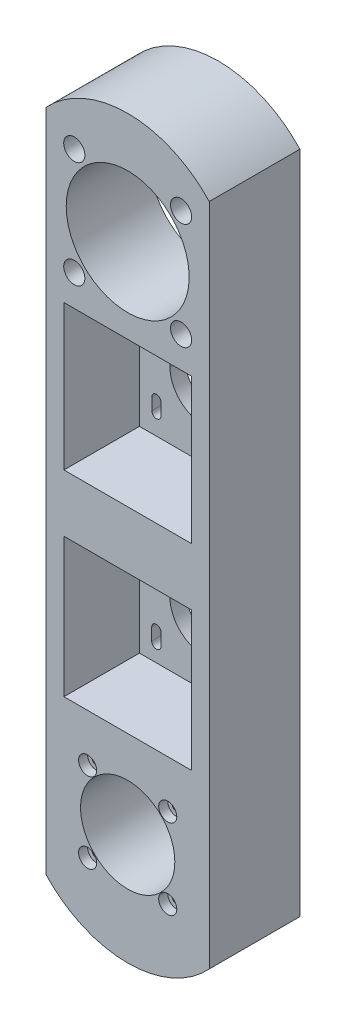
SolidWorks part; units mm, degrees
ref_plane "前视基准面" through (0, 0, 0) normal (0, 0, 1) x (1, 0, 0)
ref_plane "上视基准面" through (0, 0, 0) normal (0, 1, 0) x (1, 0, 0)
ref_plane "右视基准面" through (0, 0, 0) normal (1, 0, 0) x (0, 0, -1)
sketch "草图1" plane through (0, 0, 0) normal (0, 0, 1) x (1, 0, 0)
  line L1 (-27, 110) -> (27, 110)
  line L2 (-27, 110) -> (-27, -110)
  line L3 (-27, -110) -> (27, -110)
  line L4 (27, 110) -> (27, -110)
  line L5 (0, -110) -> (0, 110) construction
  line L6 (-27, 0) -> (27, 0) construction
  point P0 (0, 0)
  dimension "D1" = 220
  dimension "D2" = 54
extrude "凸台-拉伸1" add sketch "草图1" along normal blind 30
sketch "草图2" plane through (0, 0, 30) normal (0, 0, 1) x (1, 0, 0)
  line L0 (0, 99) -> (0, -113.7312) construction
  line L1 (-21.1, 57) -> (21.1, 57)
  line L2 (-21.1, 57) -> (-21.1, 9)
  line L3 (-21.1, 9) -> (21.1, 9)
  line L4 (21.1, 57) -> (21.1, 9)
  line L5 (0, 9) -> (0, 57) construction
  line L6 (-21.1, 33) -> (21.1, 33) construction
  line L7 (27, 110) -> (-27, 110) construction
  line L12 (0, 53) -> (0, 95) construction
  line L13 (-21, 85) -> (21, 85) construction
  point P0 (0, 33)
  point P6 (0, 85)
  dimension "D1" = 48
  dimension "D2" = 42.2
  dimension "D3" = 25
  dimension "D4" = 52
extrude "切除-拉伸1" cut sketch "草图2" against normal offset from surface (25 mm away) 5 up to face at (0, 0, 0)
sketch "草图3" plane through (0, 0, 30) normal (0, 0, -1) x (-1, 0, 0)
  line L0 (0, 105.3067) -> (0, -113.1294) construction
  line L1 (-21.1, -10) -> (21.1, -10)
  line L2 (-21.1, -10) -> (-21.1, -56)
  line L3 (-21.1, -56) -> (21.1, -56)
  line L4 (21.1, -10) -> (21.1, -56)
  line L5 (0, -56) -> (0, -10) construction
  line L6 (-21.1, -33) -> (21.1, -33) construction
  line L7 (27, -110) -> (-27, -110) construction
  line L12 (0, -95) -> (0, -53) construction
  line L13 (-21, -85) -> (21, -85) construction
  point P0 (0, -33)
  point P6 (0, -85)
  dimension "D1" = 46
  dimension "D2" = 42.2
  dimension "D3" = 25
  dimension "D4" = 52
extrude "切除-拉伸2" cut sketch "草图3" along normal offset from surface (25 mm away) 5 up to face at (0, 0, 0)
sketch "草图4" plane through (0, 0, 5) normal (0, 0, 1) x (1, 0, 0)
  line L0 (0, 33) -> (40.432, 33) construction
  line L1 (0, 0) -> (0, -107.9783) construction
  line L2 (-21.1, 57) -> (21.1, 57) construction
  line L3 (-21.1, 9) -> (21.1, 57) construction
  line L4 (21.1, 57) -> (21.1, 9) construction
  line L5 (-21.1, 57) -> (21.1, 9) construction
  line L6 (0, 35) -> (0, 31) construction
  line L7 (11, 35) -> (11, 31)
  line L8 (-11, 35) -> (-11, 31)
  line L9 (-15.5, 50.5) -> (-15.5, 46.5) construction
  line L10 (-14, 50.5) -> (-14, 46.5)
  line L11 (-17, 50.5) -> (-17, 46.5)
  line L12 (0, 33) -> (0, 63.0659) construction
  line L14 (15.5, 50.5) -> (15.5, 46.5) construction
  line L15 (14, 50.5) -> (14, 46.5)
  line L16 (17, 50.5) -> (17, 46.5)
  line L17 (15.5, 15.5) -> (15.5, 19.5) construction
  line L18 (14, 15.5) -> (14, 19.5)
  line L19 (17, 15.5) -> (17, 19.5)
  line L20 (-15.5, 15.5) -> (-15.5, 19.5) construction
  line L21 (-14, 15.5) -> (-14, 19.5)
  line L22 (-17, 15.5) -> (-17, 19.5)
  arc A17 (11, 35) -> (-11, 35) centre (0, 35) ccw
  arc A18 (-11, 31) -> (11, 31) centre (0, 31) ccw
  arc A19 (-14, 50.5) -> (-17, 50.5) centre (-15.5, 50.5) ccw
  arc A20 (-17, 46.5) -> (-14, 46.5) centre (-15.5, 46.5) ccw
  arc A21 (14, 50.5) -> (17, 50.5) centre (15.5, 50.5) cw
  arc A22 (17, 46.5) -> (14, 46.5) centre (15.5, 46.5) cw
  arc A23 (14, 15.5) -> (17, 15.5) centre (15.5, 15.5) ccw
  arc A24 (17, 19.5) -> (14, 19.5) centre (15.5, 19.5) ccw
  arc A25 (-14, 15.5) -> (-17, 15.5) centre (-15.5, 15.5) cw
  arc A26 (-17, 19.5) -> (-14, 19.5) centre (-15.5, 19.5) cw
  point P12 (0, 33)
  point P15 (0, 33)
  point P22 (-15.5, 48.5)
  point P32 (15.5, 48.5)
  point P39 (15.5, 17.5)
  point P46 (-15.5, 17.5)
  dimension "D1" = 4
  dimension "D4" = 4
  dimension "D3" = 1.5
  dimension "D6" = 11
  dimension "D2" = 15.5
  dimension "D5" = 15.5
extrude "切除-拉伸3" cut sketch "草图4" against normal through all
sketch "草图18" plane through (0, 0, 0) normal (0, 0, 1) x (1, 0, 0)
  line L1 (-16.1, -68.9) -> (16.1, -68.9)
  line L2 (-16.1, -68.9) -> (-16.1, -101.1)
  line L3 (-16.1, -101.1) -> (16.1, -101.1)
  line L4 (16.1, -68.9) -> (16.1, -101.1)
  line L5 (0, -101.1) -> (0, -68.9) construction
  line L6 (-16.1, -85) -> (16.1, -85) construction
  point P0 (0, -85)
  dimension "D1" = 32.2
  dimension "D2" = 32.2
sketch "草图26" plane through (0, 0, 5) normal (0, 0, 1) x (1, 0, 0)
  line L0 (-21.1, -56) -> (21.1, -10) construction
  line L1 (-21.1, -10) -> (21.1, -56) construction
  line L2 (0, -31) -> (0, -35) construction
  line L3 (21.1, -33) -> (-21.1, -33) construction
  line L4 (0, 99) -> (0, -113.7312) construction
  line L5 (11, -31) -> (11, -35)
  line L6 (-11, -31) -> (-11, -35)
  line L7 (-15.5, -15.5) -> (-15.5, -19.5) construction
  line L8 (-13.95, -15.5) -> (-13.95, -19.5)
  line L9 (-17.05, -15.5) -> (-17.05, -19.5)
  line L10 (0, -33) -> (45.7169, -33) construction
  line L11 (0, -33) -> (0, -41.2979) construction
  line L12 (-15.5, -50.5) -> (-15.5, -46.5) construction
  line L13 (-13.95, -50.5) -> (-13.95, -46.5)
  line L14 (-17.05, -50.5) -> (-17.05, -46.5)
  line L15 (15.5, -50.5) -> (15.5, -46.5) construction
  line L16 (13.95, -50.5) -> (13.95, -46.5)
  line L17 (17.05, -50.5) -> (17.05, -46.5)
  line L18 (15.5, -15.5) -> (15.5, -19.5) construction
  line L19 (13.95, -15.5) -> (13.95, -19.5)
  line L20 (17.05, -15.5) -> (17.05, -19.5)
  arc A0 (11, -31) -> (-11, -31) centre (0, -31) ccw
  arc A1 (-11, -35) -> (11, -35) centre (0, -35) ccw
  arc A2 (-13.95, -15.5) -> (-17.05, -15.5) centre (-15.5, -15.5) ccw
  arc A3 (-17.05, -19.5) -> (-13.95, -19.5) centre (-15.5, -19.5) ccw
  arc A4 (-13.95, -50.5) -> (-17.05, -50.5) centre (-15.5, -50.5) cw
  arc A5 (-17.05, -46.5) -> (-13.95, -46.5) centre (-15.5, -46.5) cw
  arc A6 (13.95, -50.5) -> (17.05, -50.5) centre (15.5, -50.5) ccw
  arc A7 (17.05, -46.5) -> (13.95, -46.5) centre (15.5, -46.5) ccw
  arc A8 (13.95, -15.5) -> (17.05, -15.5) centre (15.5, -15.5) cw
  arc A9 (17.05, -19.5) -> (13.95, -19.5) centre (15.5, -19.5) cw
  point P8 (0, -33)
  point P16 (0, -33)
  point P23 (-15.5, -17.5)
  point P34 (-15.5, -48.5)
  point P41 (15.5, -48.5)
  point P48 (15.5, -17.5)
  dimension "D2" = 11
  dimension "D4" = 1.55
  dimension "D1" = 4
  dimension "D3" = 4
  dimension "D5" = 15.5
  dimension "D6" = 15.5
extrude "切除-拉伸13" cut sketch "草图26" against normal through all
extrude "切除-拉伸9" cut sketch "草图18" along normal blind 6
sketch "草图9" plane through (0, 0, 6) normal (0, 0, 1) x (1, 0, 0)
  line L0 (16.1, -85) -> (-16.1, -85) construction
  line L3 (0, -68.9) -> (0, -101.1) construction
  line L6 (-16.1, -68.9) -> (16.1, -68.9) construction
  line L8 (16.1, -101.1) -> (-16.1, -101.1) construction
  line L9 (-16.1, -101.1) -> (-16.1, -68.9) construction
  line L10 (16.1, -68.9) -> (16.1, -101.1) construction
  circle A1 centre (0, -85) radius 15.6
  circle A2 centre (-13.2583, -71.7417) radius 1.6
  circle A3 centre (13.2583, -71.7417) radius 1.6
  circle A4 centre (13.2583, -98.2583) radius 1.6
  circle A5 centre (-13.2583, -98.2583) radius 1.6
  point P26 (0, -85)
  dimension "D1" = 31.2
  dimension "D2" = 3.2
  dimension "D3" = 18.75
  dimension "D5" = 4
extrude "切除-拉伸4" cut sketch "草图9" along normal through all
sketch "草图16" plane through (0, 0, 0) normal (0, 0, 1) x (1, 0, 0)
  line L1 (-21.35, 106.35) -> (21.35, 106.35)
  line L2 (-21.35, 106.35) -> (-21.35, 63.65)
  line L3 (-21.35, 63.65) -> (21.35, 63.65)
  line L4 (21.35, 106.35) -> (21.35, 63.65)
  line L5 (0, 63.65) -> (0, 106.35) construction
  line L6 (-21.35, 85) -> (21.35, 85) construction
  point P0 (0, 85)
  dimension "D1" = 42.7
  dimension "D2" = 42.7
extrude "切除-拉伸7" cut sketch "草图16" along normal blind 2.5
sketch "草图13" plane through (0, 0, 2.5) normal (0, 0, -1) x (-1, 0, 0)
  line L0 (21.35, 85) -> (-21.35, 85) construction
  line L1 (-27, 110) -> (27, 110) construction
  line L2 (0, 85) -> (0, 93.445) construction
  line L3 (21.35, 63.65) -> (21.35, 106.35) construction
  line L4 (27, 110) -> (27, -110) construction
  line L5 (-27, -110) -> (-27, 110) construction
  line L6 (-21.35, 106.35) -> (-21.35, 63.65) construction
  line L7 (0, 106.35) -> (0, 63.65) construction
  line L8 (21.35, 106.35) -> (-21.35, 106.35) construction
  line L9 (-21.35, 63.65) -> (21.35, 63.65) construction
  circle A0 centre (0, 85) radius 20.35
  circle A1 centre (-17.6777, 102.6777) radius 2.1
  circle A2 centre (17.6777, 102.6777) radius 2.1
  circle A3 centre (17.6777, 67.3223) radius 2.1
  circle A4 centre (-17.6777, 67.3223) radius 2.1
  point P25 (0, 85)
  dimension "D1" = 40.7
  dimension "D2" = 4.2
  dimension "D3" = 25
  dimension "D6" = 25
  dimension "D5" = 4
extrude "切除-拉伸6" cut sketch "草图13" against normal through all
sketch "草图15" plane through (0, 0, 0) normal (0, 0, -1) x (-1, 0, 0)
  line L0 (-27, 110) -> (27, 110) construction
  line L1 (-27, 110) -> (27, 110)
  arc A0 (-27, 110) -> (27, 110) centre (0, 85) cw
  point P6 (0, 0)
extrude "凸台-拉伸3" add sketch "草图15" against normal up to surface (30 mm away) up to face at (15.5777, 67.3223, 30)
sketch "草图17" plane through (0, 0, 0) normal (0, 0, -1) x (-1, 0, 0)
  line L0 (0, 99) -> (0, -113.7312) construction
  circle A0 centre (-24, 100) radius 1.5
  circle A1 centre (24, 100) radius 1.5
  circle A2 centre (24, 66) radius 1.5
  circle A3 centre (-24, 66) radius 1.5
  dimension "D1" = 3
  dimension "D2" = 10
  dimension "D3" = 24
  dimension "D4" = 2
  dimension "D5" = 2
extrude "切除-拉伸8" cut sketch "草图17" against normal blind 8
fillet "圆角1" [suppressed] radius 10
sketch "草图21" plane through (0, 0, 30) normal (0, 0, 1) x (1, 0, 0)
  circle A0 centre (-17.6777, 102.6777) radius 3.5
  circle A1 centre (17.6777, 102.6777) radius 3.5
  circle A2 centre (17.6777, 67.3223) radius 3.5
  circle A3 centre (-17.6777, 67.3223) radius 3.5
  point P12 (0, 85)
  dimension "D1" = 7
  dimension "D2" = 4
extrude "切除-拉伸11" cut sketch "草图21" against normal blind 7.5 and the other way through all
sketch "草图28" plane through (0, 0, 30) normal (0, 0, 1) x (1, 0, 0)
  line L0 (0, 99) -> (0, -113.7312) construction
  line L1 (-27, -110) -> (27, -110) construction
  line L2 (-27, -110) -> (27, -110)
  arc A0 (-27, -110) -> (27, -110) centre (0, -84.9952) ccw
  dimension "D1" = 36.8
extrude "凸台-拉伸4" add sketch "草图28" against normal up to surface (30 mm away) up to face at (22.5, 66, 0)
sketch "草图29" plane through (0, 0, 30) normal (0, 0, 1) x (1, 0, 0)
  circle A0 centre (-13.2583, -71.7417) radius 3
  circle A1 centre (13.2583, -71.7417) radius 3
  circle A2 centre (13.2583, -98.2583) radius 3
  circle A3 centre (-13.2583, -98.2583) radius 3
  point P12 (0, -85)
  dimension "D1" = 6
  dimension "D2" = 4
extrude "切除-拉伸15" cut sketch "草图29" against normal blind 3
sketch "草图30" plane through (0, 0, 0) normal (0, 0, -1) x (-1, 0, 0)
  line L0 (0, 99) -> (0, -113.7312) construction
  circle A0 centre (-24, -100) radius 1.5
  circle A1 centre (-24, -66) radius 1.5
  circle A2 centre (24, -66) radius 1.5
  circle A3 centre (24, -100) radius 1.5
  dimension "D1" = 3
  dimension "D2" = 10
  dimension "D3" = 24
  dimension "D4" = 2
  dimension "D5" = 2
extrude "切除-拉伸16" cut sketch "草图30" against normal blind 8
sketch "草图31" plane through (0, 0, 0) normal (0, 0, -1) x (-1, 0, 0)
  line L1 (-33.0543, -60.0516) -> (30.9302, -60.0516)
  line L2 (-33.0543, -60.0516) -> (-33.0543, -107.6777)
  line L3 (-33.0543, -107.6777) -> (30.9302, -107.6777)
  line L4 (30.9302, -60.0516) -> (30.9302, -107.6777)
